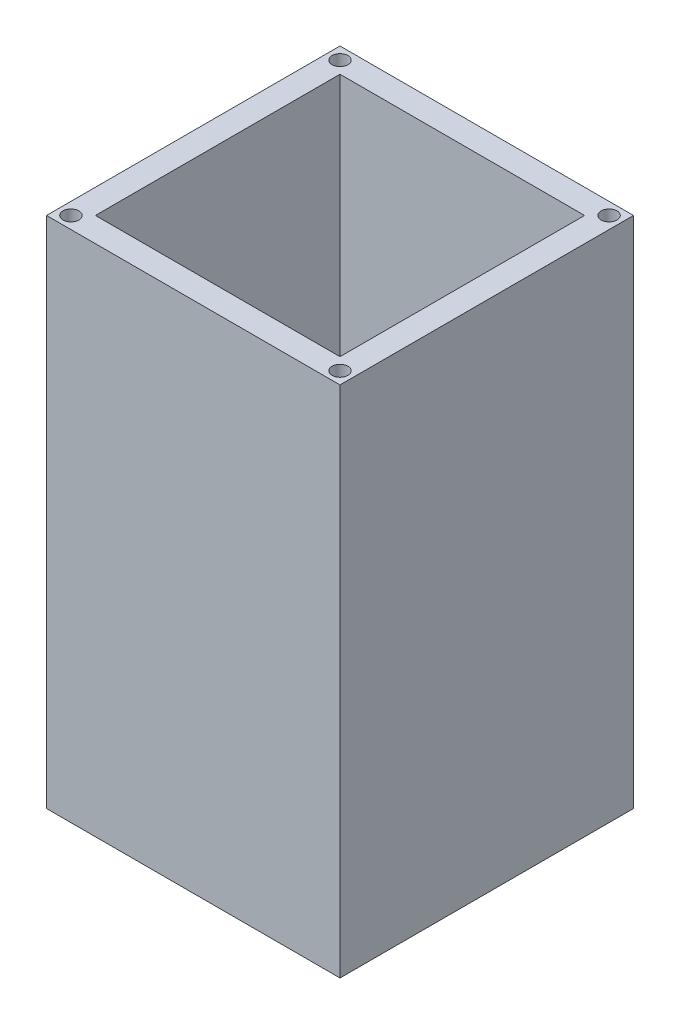
SolidWorks part; units mm, degrees
ref_plane "Front Plane" through (0, 0, 0) normal (0, 0, 1) x (1, 0, 0)
ref_plane "Top Plane" through (0, 0, 0) normal (0, 1, 0) x (1, 0, 0)
ref_plane "Right Plane" through (0, 0, 0) normal (1, 0, 0) x (0, 0, -1)
sketch "Sketch1" plane through (0, 0, 0) normal (0, 1, 0) x (1, 0, 0)
  line L1 (0, 0) -> (120, 0)
  line L2 (0, 0) -> (0, 120)
  line L3 (0, 120) -> (120, 120)
  line L4 (120, 0) -> (120, 120)
  circle A0 centre (60, 60) radius 7.5
  point P9 (75.8432, 38.2044)
  dimension "D5" = 15
  dimension "D1" = 120
  dimension "D2" = 120
  dimension "D3" = 60
  dimension "D4" = 60
extrude "Boss-Extrude1" add sketch "Sketch1" along normal blind 10
sketch3d "3DSketch1"
  line L0 (110, 10, -10) -> (110, 10, -110)
  line L1 (110, 10, -110) -> (10, 10, -110)
  line L2 (10, 10, -110) -> (10, 10, -10)
  line L3 (10, 10, -10) -> (110, 10, -10)
  line L4 (110, 10, -10) -> (110, 10, -110)
  line L5 (110, 10, -110) -> (10, 10, -110)
  line L6 (10, 10, -110) -> (10, 10, -10)
  line L7 (10, 10, -10) -> (110, 10, -10)
  line L8 (0, 10, -120) -> (0, 10, 0)
  line L9 (0, 10, 0) -> (120, 10, 0)
  line L10 (120, 10, 0) -> (120, 10, -120)
  line L11 (120, 10, -120) -> (0, 10, -120)
  dimension "D1" = 10
extrude "Boss-Extrude2" add sketch "3DSketch1" along direction (0, -1, 0) on the side of the normal blind 200
sketch "Sketch2" plane through (0, 210, 0) normal (0, 1, 0) x (1, 0, 0)
  line L0 (120, 120) -> (0, 120) construction
  line L1 (120, 0) -> (120, 120) construction
  line L2 (0, 120) -> (0, 0) construction
  line L3 (0, 0) -> (120, 0) construction
  circle A0 centre (115, 115) radius 3.25
  circle A1 centre (5, 115) radius 3.25
  circle A2 centre (115, 5) radius 3.25
  circle A3 centre (5, 5) radius 3.25
  point P12 (5.1639, 115)
  point P15 (115, 4.2541)
  point P18 (5, 5)
  dimension "D1" = 5
  dimension "D2" = 5
  dimension "D3" = 5
  dimension "D4" = 5
  dimension "D5" = 5
extrude "Cut-Extrude1" cut sketch "Sketch2" against normal blind 15
